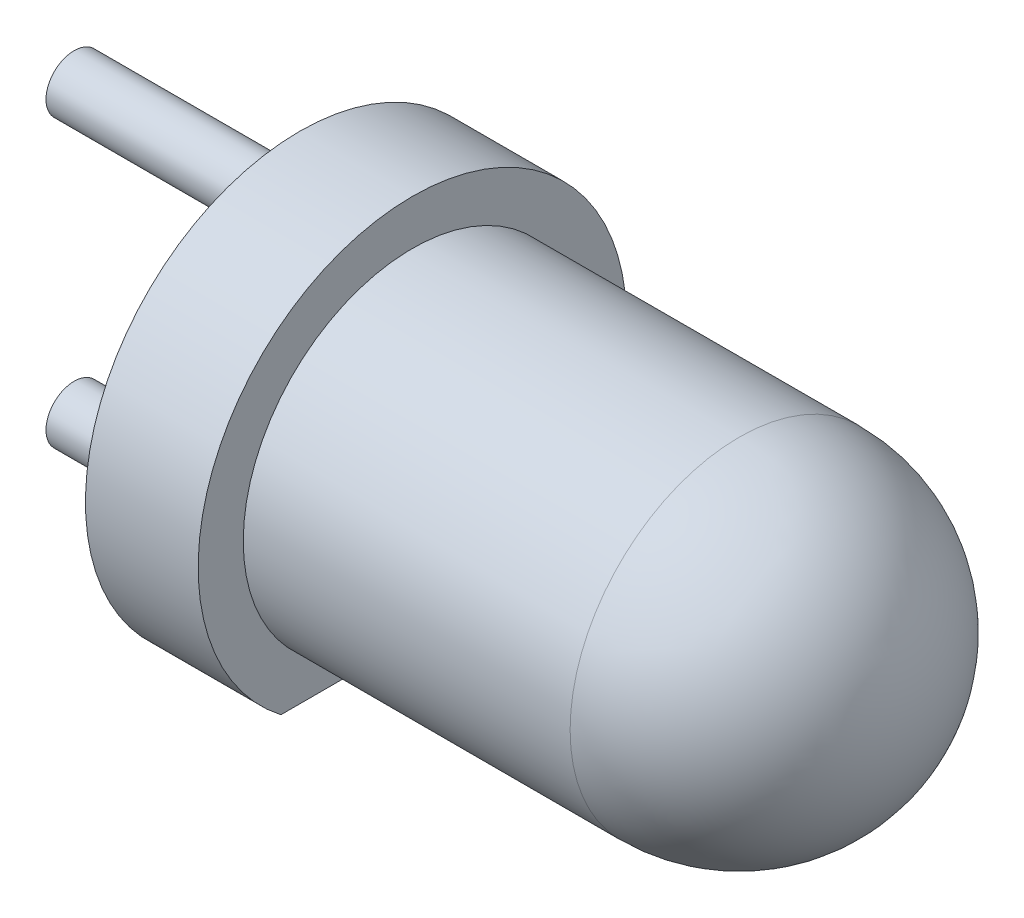
SolidWorks part; units mm, degrees
ref_plane "Plan de face" through (0, 0, 0) normal (0, 0, 1) x (1, 0, 0)
ref_plane "Plan de dessus" through (0, 0, 0) normal (0, 1, 0) x (1, 0, 0)
ref_plane "Plan de droite" through (0, 0, 0) normal (1, 0, 0) x (0, 0, -1)
sketch "Esquisse1" plane through (0, 0, 0) normal (0, 0, 1) x (1, 0, 0)
  line L1 (0, 0) -> (4.4, 0)
  line L3 (0, 1.5) -> (2.9, 1.5)
  line L5 (0, 0) -> (-1, 0)
  line L6 (0, 1.5) -> (0, 1.9)
  line L7 (0, 1.9) -> (-1, 1.9)
  line L8 (-1, 0) -> (-1, 1.9)
  arc A0 (4.4, 0) -> (2.9, 1.5) centre (2.9, 0) ccw
  dimension "D1" = 1.5
  dimension "D2" = 2.9
  dimension "D3" = 2.9
  dimension "D4" = 1
  dimension "D5" = 1.9
revolve "Révolution1" add sketch "Esquisse1" angle 360 about L1
sketch "Esquisse2" plane through (-1, 0, 0) normal (-1, 0, 0) x (0, 0, 1)
  circle A0 centre (0, 1.27) radius 0.25
  circle A1 centre (0, -1.27) radius 0.25
  dimension "D1" = 1.27
  dimension "D2" = 2.54
extrude "Extrusion1" add sketch "Esquisse2" along normal blind 2
sketch "Esquisse3" plane through (-1, 0, 0) normal (-1, 0, 0) x (0, 0, 1)
  line L1 (-1.8671, -1.5) -> (1.9356, -1.5)
  line L2 (-1.8671, -1.5) -> (-1.8671, -2.2173)
  line L3 (-1.8671, -2.2173) -> (1.9356, -2.2173)
  line L4 (1.9356, -1.5) -> (1.9356, -2.2173)
  dimension "D1" = 1.5
extrude "Enlèv. mat.-Extru.1" cut sketch "Esquisse3" against normal blind 4
